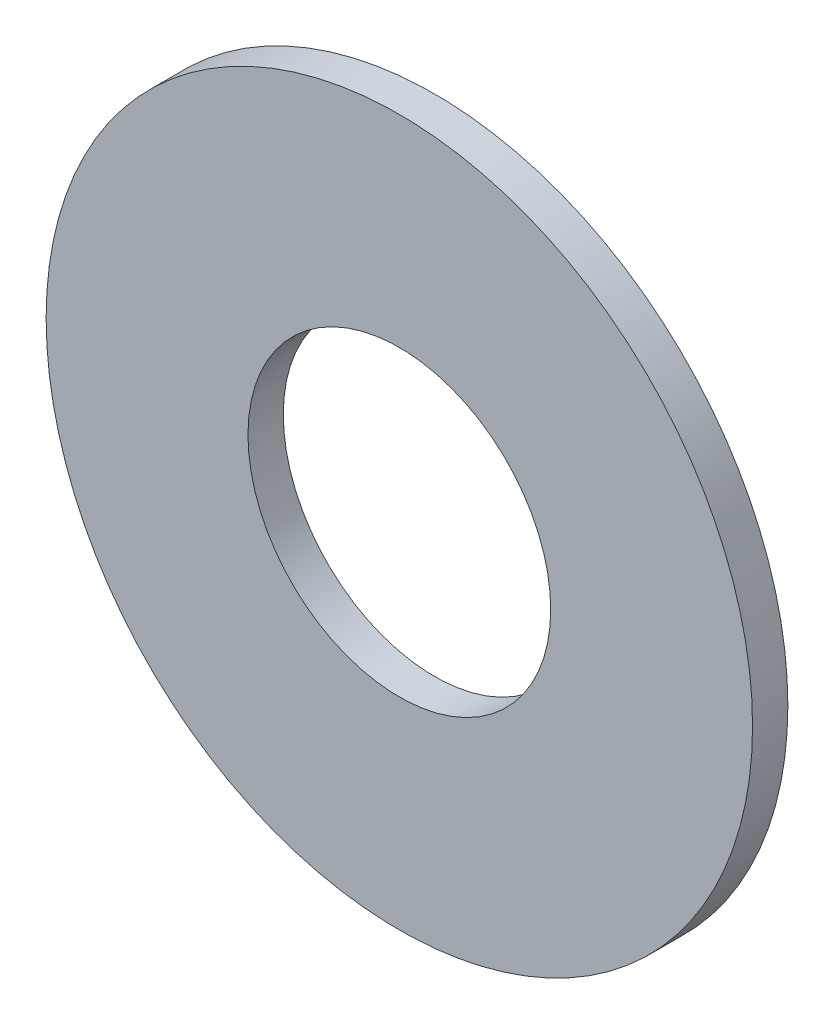
SolidWorks part; units mm, degrees
ref_plane "Plan de face" through (0, 0, 0) normal (0, 0, 1) x (1, 0, 0)
ref_plane "Plan de dessus" through (0, 0, 0) normal (0, 1, 0) x (1, 0, 0)
ref_plane "Plan de droite" through (0, 0, 0) normal (1, 0, 0) x (0, 0, -1)
sketch "Esquisse1" plane through (0, 0, 0) normal (0, 0, 1) x (1, 0, 0)
  circle A0 centre (0, 0) radius 7
  dimension "D1" = 14
extrude "Boss.-Extru.1" add sketch "Esquisse1" along normal blind 0.7
sketch "Esquisse2" plane through (0, 0, 0.7) normal (0, 0, 1) x (1, 0, 0)
  circle A0 centre (0, 0) radius 3
  dimension "D1" = 6
extrude "Enlèv. mat.-Extru.1" cut sketch "Esquisse2" against normal blind 1.5
